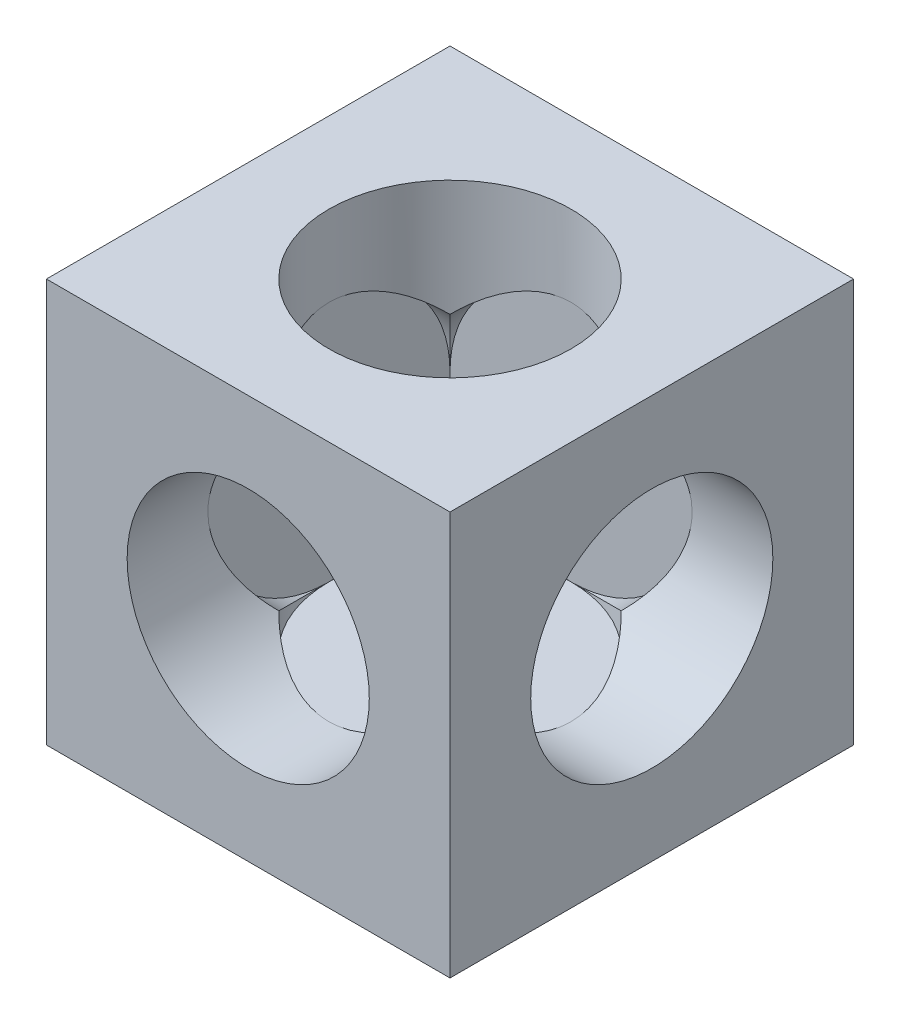
SolidWorks part; units mm, degrees
material "1060 Сплав"
ref_plane "Piano frontale" through (0, 0, 0) normal (0, 0, 1) x (1, 0, 0)
ref_plane "Piano superiore" through (0, 0, 0) normal (0, 1, 0) x (1, 0, 0)
ref_plane "Piano destro" through (0, 0, 0) normal (1, 0, 0) x (0, 0, -1)
sketch "Schizzo1" plane through (0, 0, 0) normal (0, 0, 1) x (1, 0, 0)
  line L1 (5, -5) -> (-5, -5)
  line L2 (5, -5) -> (5, 5)
  line L3 (5, 5) -> (-5, 5)
  line L4 (-5, -5) -> (-5, 5)
  line L5 (5, -5) -> (-5, 5) construction
  line L6 (5, 5) -> (-5, -5) construction
  point P0 (0, 0)
  dimension "D1" = 10
extrude "Estrusione-Estrusione1" add sketch "Schizzo1" along normal blind 10
hole_wizard "Foro filettato M3x0.5-1" positions "Schizzo3" profile "Schizzo2" tap size "M3x0.5" standard "Ansi Metric" end condition through all
sketch "Schizzo3" plane through (0, 0, 10) normal (0, 0, 1) x (1, 0, 0)
  point P0 (0, 0)
sketch "Schizzo2" plane through (0, 0, 10) normal (1, 0, 0) x (0, -1, 0)
  line L0 (0, 0) -> (0, 10)
  line L1 (0, 10) -> (1.25, 10)
  line L2 (1.25, 10) -> (1.25, 0)
  line L5 (1.25, 0) -> (0, 0)
  line L11 (0, -6.35) -> (0, 107.95) construction
  dimension "Thread Major Dia." = 2.5
  dimension "Thru Tap Drill Depth" = 10
hole_wizard "Foro filettato M3x0.5-2" positions "Schizzo5" profile "Schizzo4" tap size "M3x0.5" standard "Ansi Metric" end condition through all
sketch "Schizzo5" plane through (5, 0, 0) normal (1, 0, 0) x (0, 0, -1)
  point P0 (-5, 0)
sketch "Schizzo4" plane through (5, 0, 5) normal (0, 1, 0) x (0, 0, -1)
  line L0 (0, 0) -> (0, 10)
  line L1 (0, 10) -> (1.25, 10)
  line L2 (1.25, 10) -> (1.25, 0)
  line L5 (1.25, 0) -> (0, 0)
  line L11 (0, -6.35) -> (0, 107.95) construction
  dimension "Thread Major Dia." = 2.5
  dimension "Thru Tap Drill Depth" = 10
hole_wizard "Foro filettato M3x0.5-3" positions "Schizzo7" profile "Schizzo6" tap size "M3x0.5" standard "Ansi Metric" end condition through all
sketch "Schizzo7" plane through (0, -5, 0) normal (0, -1, 0) x (-1, 0, 0)
  point P0 (0, -5)
sketch "Schizzo6" plane through (0, -5, 5) normal (1, 0, 0) x (0, 0, -1)
  line L0 (0, 0) -> (0, 10)
  line L1 (0, 10) -> (1.25, 10)
  line L2 (1.25, 10) -> (1.25, 0)
  line L5 (1.25, 0) -> (0, 0)
  line L11 (0, -6.35) -> (0, 107.95) construction
  dimension "Thread Major Dia." = 2.5
  dimension "Thru Tap Drill Depth" = 10
sketch "Schizzo8" plane through (0, 0, 10) normal (0, 0, 1) x (1, 0, 0)
  circle A0 centre (0, 0) radius 3
  dimension "D1" = 6
extrude "Taglio-Estrusione1" cut sketch "Schizzo8" against normal blind 8
sketch "Schizzo9" plane through (5, 0, 0) normal (1, 0, 0) x (0, 0, -1)
  circle A0 centre (-5, 0) radius 3
  dimension "D1" = 6
extrude "Taglio-Estrusione2" cut sketch "Schizzo9" against normal blind 8
sketch "Schizzo10" plane through (0, 5, 0) normal (0, 1, 0) x (1, 0, 0)
  circle A0 centre (0, -5) radius 3
  dimension "D1" = 6
extrude "Taglio-Estrusione3" cut sketch "Schizzo10" against normal blind 8
